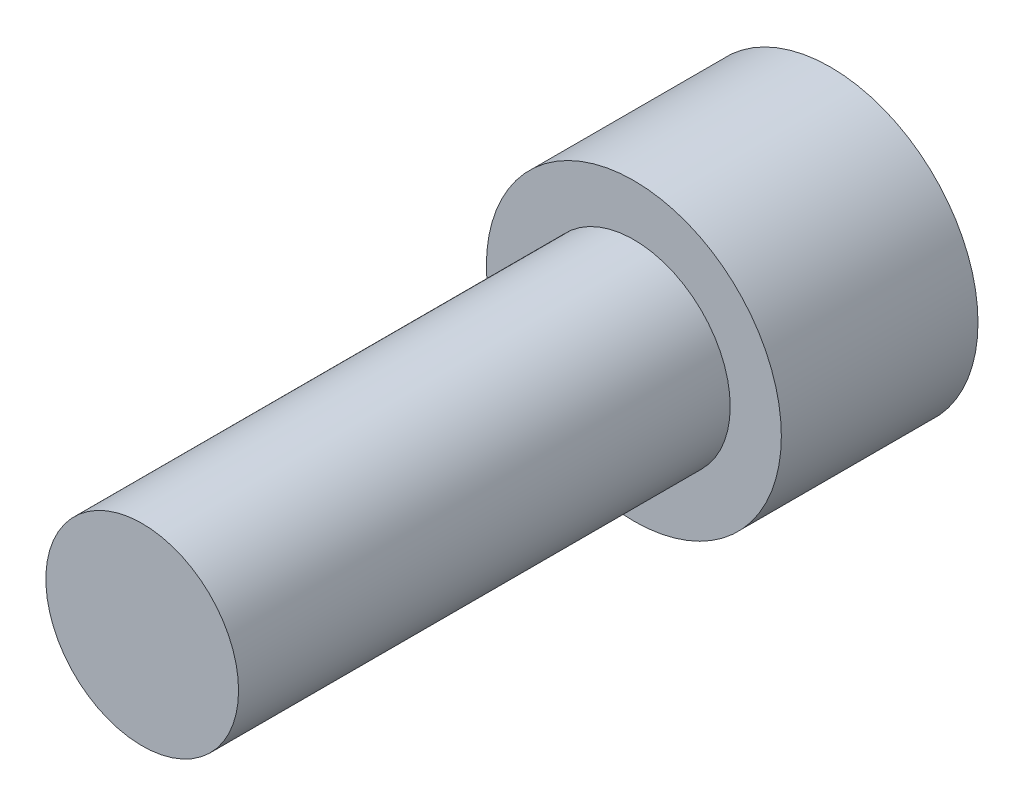
SolidWorks part; units mm, degrees
ref_plane "Front Plane" through (0, 0, 0) normal (0, 0, 1) x (1, 0, 0)
ref_plane "Top Plane" through (0, 0, 0) normal (0, 1, 0) x (1, 0, 0)
ref_plane "Right Plane" through (0, 0, 0) normal (1, 0, 0) x (0, 0, -1)
sketch "Sketch1" plane through (0, 0, 0) normal (0, 0, 1) x (1, 0, 0)
  circle A0 centre (0, 0) radius 3.81
extrude "Extrude1" add sketch "Sketch1" along normal blind 17.78
sketch "Sketch2" plane through (0, 0, 17.78) normal (0, 0, 1) x (1, 0, 0)
  circle A0 centre (0, 0) radius 2.4892
extrude "Extrude2" cut sketch "Sketch2" against normal blind 12.7 flip side to cut
sketch "Sketch3" plane through (0, 0, 0) normal (0, 0, -1) x (-1, 0, 0)
  line L1 (0, 2.9877) -> (-2.5874, 1.4938)
  line L2 (-2.5874, 1.4938) -> (-2.5874, -1.4938)
  line L3 (-2.5874, -1.4938) -> (0, -2.9877)
  line L4 (0, -2.9877) -> (2.5874, -1.4938)
  line L5 (2.5874, -1.4938) -> (2.5874, 1.4938)
  line L6 (2.5874, 1.4938) -> (0, 2.9877)
  circle A0 centre (0, 0) radius 2.5874 construction
extrude "Extrude3" cut sketch "Sketch3" against normal blind 3.048
